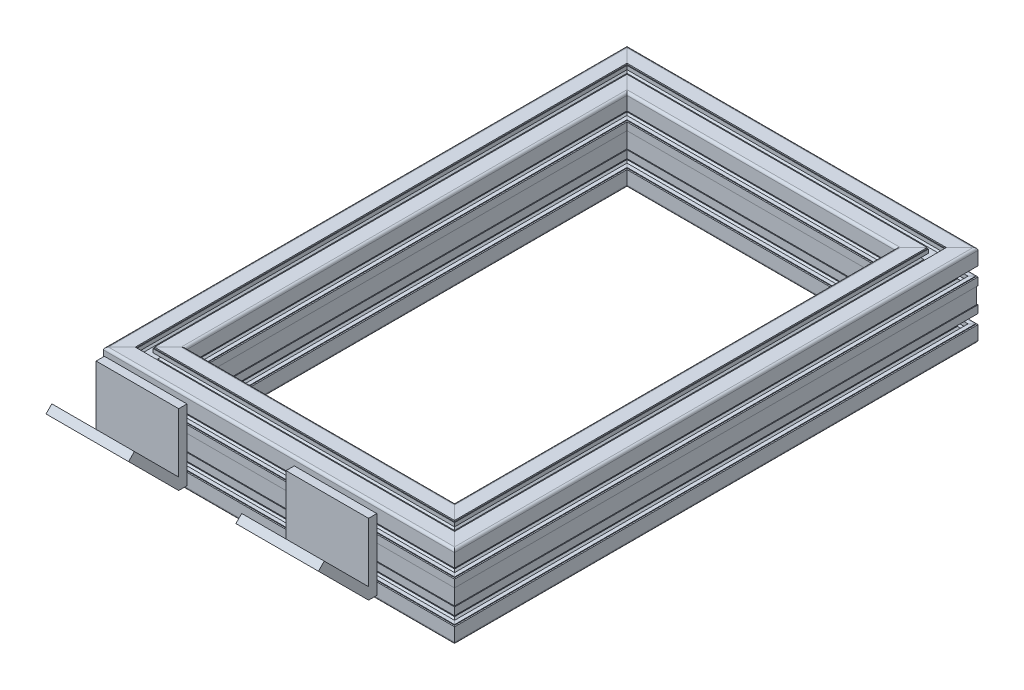
SolidWorks part; units mm, degrees
ref_plane "Plano frontal" through (0, 0, 0) normal (0, 0, 1) x (1, 0, 0)
ref_plane "Plano superior" through (0, 0, 0) normal (0, 1, 0) x (1, 0, 0)
ref_plane "Plano direito" through (0, 0, 0) normal (1, 0, 0) x (0, 0, -1)
sketch3d "3DSketch1"
  line L0 (-22674.7588, 3641.8152, 40199.9002) -> (-22776.7588, 3641.8152, 40199.9002) construction
  line L1 (-22674.7588, 12271.8152, 40199.9002) -> (-22674.7588, -2728.1848, 40199.9002) construction
  line L2 (-22776.7588, 12271.8152, 40199.9002) -> (-22776.7588, -2728.1848, 40199.9002) construction
  line L3 (-22676.9563, 3641.8152, 40224.9002) -> (-22676.9563, 3641.8152, 40808.9455)
  line L4 (-22676.9563, 3641.8152, 40808.9455) -> (-23052.1444, 3641.8152, 40808.9455)
  line L5 (-23052.1444, 3641.8152, 40808.9455) -> (-23052.1444, 3641.8152, 40224.9002)
  line L6 (-22676.9563, 3641.8152, 40224.9002) -> (-23052.1444, 3641.8152, 40224.9002)
  line L7 (-22872.616, 3641.8152, 40199.9002) -> (-22872.616, 3641.8152, 40224.9002) construction
  line L8 (-22776.9563, 3641.8152, 40706.6002) -> (-22776.9563, 3641.8152, 40224.9002) construction
  line L9 (-22776.9563, 11646.2158, 40706.6002) -> (-22776.9563, -2011.9888, 40706.6002) construction
  line L10 (-22902.1444, 3641.8152, 40306.6002) -> (-22902.1444, 3641.8152, 40224.9002) construction
  line L12 (-22776.9563, 3641.8152, 40706.6002) -> (-22902.1444, 3641.8152, 40706.6002) construction
  line L13 (-22902.1444, 3641.8152, 40706.6002) -> (-22902.1444, 3641.8152, 40306.6002) construction
  line L14 (-22902.1444, 11499.48, 40306.6002) -> (-22902.1444, -1887.3148, 40306.6002) construction
  dimension "D1" = 25
  dimension "D2" = 100
  dimension "D3" = 150
other "Aluminium profile 50x100 50X100(1)"
ref_plane "Plane1" through (-22676.9563, 3641.8152, 40224.9002) normal (0, 0, 1) x (1, 0, 0)
sketch "Sketch1" plane through (-22676.9563, 3641.8152, 40224.9002) normal (0, 0, 1) x (1, 0, 0)
  line L0 (15.1906, 37.8447) -> (11.8847, 34.5389)
  line L1 (11.8847, 34.5389) -> (9.5389, 36.8847)
  line L2 (9.5389, 36.8847) -> (12.8447, 40.1906)
  line L3 (11.2262, 45.7) -> (9.5, 45.7)
  line L4 (9.5, 45.7) -> (9.5, 48.3)
  line L5 (9.5, 48.3) -> (19, 48.3)
  line L6 (19, 48.3) -> (19, 47.2697)
  line L7 (22.2697, 44) -> (23.3, 44)
  line L8 (23.3, 44) -> (23.3, 34.5)
  line L9 (23.3, 34.5) -> (20.7, 34.5)
  line L10 (20.7, 34.5) -> (20.7, 36.2262)
  line L11 (12.8447, -40.1906) -> (9.5389, -36.8847)
  line L12 (9.5389, -36.8847) -> (11.8847, -34.5389)
  line L13 (11.8847, -34.5389) -> (15.1906, -37.8447)
  line L14 (20.7, -36.2262) -> (20.7, -34.5)
  line L15 (20.7, -34.5) -> (23.3, -34.5)
  line L16 (23.3, -34.5) -> (23.3, -44)
  line L17 (23.3, -44) -> (22.2697, -44)
  line L18 (19, -47.2697) -> (19, -48.3)
  line L19 (19, -48.3) -> (9.5, -48.3)
  line L20 (9.5, -48.3) -> (9.5, -45.7)
  line L21 (9.5, -45.7) -> (11.2262, -45.7)
  line L22 (-19, 48.3) -> (-9.5, 48.3)
  line L23 (-9.5, 48.3) -> (-9.5, 45.7)
  line L24 (-9.5, 45.7) -> (-11.2262, 45.7)
  line L25 (-12.8447, 40.1906) -> (-9.5389, 36.8847)
  line L26 (-9.5389, 36.8847) -> (-11.8847, 34.5389)
  line L27 (-11.8847, 34.5389) -> (-15.1906, 37.8447)
  line L28 (-20.7, 36.2262) -> (-20.7, 34.5)
  line L29 (-20.7, 34.5) -> (-23.3, 34.5)
  line L30 (-23.3, 34.5) -> (-23.3, 44)
  line L31 (-23.3, 44) -> (-22.2697, 44)
  line L32 (-19, 47.2697) -> (-19, 48.3)
  line L33 (-23.3, -34.5) -> (-20.7, -34.5)
  line L34 (-20.7, -34.5) -> (-20.7, -36.2262)
  line L35 (-15.1906, -37.8447) -> (-11.8847, -34.5389)
  line L36 (-11.8847, -34.5389) -> (-9.5389, -36.8847)
  line L37 (-9.5389, -36.8847) -> (-12.8447, -40.1906)
  line L38 (-11.2262, -45.7) -> (-9.5, -45.7)
  line L39 (-9.5, -45.7) -> (-9.5, -48.3)
  line L40 (-9.5, -48.3) -> (-19, -48.3)
  line L41 (-19, -48.3) -> (-19, -47.2697)
  line L42 (-22.2697, -44) -> (-23.3, -44)
  line L43 (-23.3, -44) -> (-23.3, -34.5)
  line L44 (-10.3, -23) -> (-10.3, -16.9877)
  line L45 (-10.3, -16.9877) -> (-8.0123, -14.7)
  line L46 (-8.0123, -14.7) -> (-2, -14.7)
  line L47 (-2, -14.7) -> (-2, -16.5539)
  line L48 (-2, -16.5539) -> (-3.5923, -17.2964)
  line L49 (-3.5923, -17.2964) -> (-2.1131, -20.4685)
  line L50 (2.1131, -20.4685) -> (3.5923, -17.2964)
  line L51 (3.5923, -17.2964) -> (2, -16.5539)
  line L52 (2, -16.5539) -> (2, -14.7)
  line L53 (2, -14.7) -> (8.0123, -14.7)
  line L54 (8.0123, -14.7) -> (10.3, -16.9877)
  line L55 (10.3, -16.9877) -> (10.3, -23)
  line L56 (10.3, -23) -> (8.4461, -23)
  line L57 (8.4461, -23) -> (7.7036, -21.4077)
  line L58 (7.7036, -21.4077) -> (4.5315, -22.8869)
  line L59 (4.5315, -27.1131) -> (7.7036, -28.5923)
  line L60 (7.7036, -28.5923) -> (8.4461, -27)
  line L61 (8.4461, -27) -> (10.3, -27)
  line L62 (10.3, -27) -> (10.3, -33.0123)
  line L63 (10.3, -33.0123) -> (8.0123, -35.3)
  line L64 (8.0123, -35.3) -> (2, -35.3)
  line L65 (2, -35.3) -> (2, -33.4461)
  line L66 (2, -33.4461) -> (3.5923, -32.7036)
  line L67 (3.5923, -32.7036) -> (2.1131, -29.5315)
  line L68 (-2.1131, -29.5315) -> (-3.5923, -32.7036)
  line L69 (-3.5923, -32.7036) -> (-2, -33.4461)
  line L70 (-2, -33.4461) -> (-2, -35.3)
  line L71 (-2, -35.3) -> (-8.0123, -35.3)
  line L72 (-8.0123, -35.3) -> (-10.3, -33.0123)
  line L73 (-10.3, -33.0123) -> (-10.3, -27)
  line L74 (-10.3, -27) -> (-8.4461, -27)
  line L75 (-8.4461, -27) -> (-7.7036, -28.5923)
  line L76 (-7.7036, -28.5923) -> (-4.5315, -27.1131)
  line L77 (-4.5315, -22.8869) -> (-7.7036, -21.4077)
  line L78 (-7.7036, -21.4077) -> (-8.4461, -23)
  line L79 (-8.4461, -23) -> (-10.3, -23)
  line L80 (8.0123, 35.3) -> (10.3, 33.0123)
  line L81 (10.3, 33.0123) -> (10.3, 27)
  line L82 (10.3, 27) -> (8.4461, 27)
  line L83 (8.4461, 27) -> (7.7036, 28.5923)
  line L84 (7.7036, 28.5923) -> (4.5315, 27.1131)
  line L85 (4.5315, 22.8869) -> (7.7036, 21.4077)
  line L86 (7.7036, 21.4077) -> (8.4461, 23)
  line L87 (8.4461, 23) -> (10.3, 23)
  line L88 (10.3, 23) -> (10.3, 16.9877)
  line L89 (10.3, 16.9877) -> (8.0123, 14.7)
  line L90 (8.0123, 14.7) -> (2, 14.7)
  line L91 (2, 14.7) -> (2, 16.5539)
  line L92 (2, 16.5539) -> (3.5923, 17.2964)
  line L93 (3.5923, 17.2964) -> (2.1131, 20.4685)
  line L94 (-2.1131, 20.4685) -> (-3.5923, 17.2964)
  line L95 (-3.5923, 17.2964) -> (-2, 16.5539)
  line L96 (-2, 16.5539) -> (-2, 14.7)
  line L97 (-2, 14.7) -> (-8.0123, 14.7)
  line L98 (-8.0123, 14.7) -> (-10.3, 16.9877)
  line L99 (-10.3, 16.9877) -> (-10.3, 23)
  line L100 (-10.3, 23) -> (-8.4461, 23)
  line L101 (-8.4461, 23) -> (-7.7036, 21.4077)
  line L102 (-7.7036, 21.4077) -> (-4.5315, 22.8869)
  line L103 (-4.5315, 27.1131) -> (-7.7036, 28.5923)
  line L104 (-7.7036, 28.5923) -> (-8.4461, 27)
  line L105 (-8.4461, 27) -> (-10.3, 27)
  line L106 (-10.3, 27) -> (-10.3, 33.0123)
  line L107 (-10.3, 33.0123) -> (-8.0123, 35.3)
  line L108 (-8.0123, 35.3) -> (-2, 35.3)
  line L109 (-2, 35.3) -> (-2, 33.4461)
  line L110 (-2, 33.4461) -> (-3.5923, 32.7036)
  line L111 (-3.5923, 32.7036) -> (-2.1131, 29.5315)
  line L112 (2.1131, 29.5315) -> (3.5923, 32.7036)
  line L113 (3.5923, 32.7036) -> (2, 33.4461)
  line L114 (2, 33.4461) -> (2, 35.3)
  line L115 (2, 35.3) -> (8.0123, 35.3)
  line L116 (21, 12.45) -> (21, -12.45)
  line L117 (21, -12.45) -> (-21, -12.45)
  line L118 (-21, -12.45) -> (-21, 12.45)
  line L119 (-21, 12.45) -> (21, 12.45)
  line L120 (23.5, -30) -> (19, -30)
  line L121 (19, -30) -> (19, -35.05)
  line L122 (19, -35.05) -> (14.8, -35.05)
  line L123 (14.8, -35.05) -> (12.5, -32.75)
  line L124 (12.5, -32.75) -> (12.5, -17.25)
  line L125 (12.5, -17.25) -> (14.8, -14.95)
  line L126 (14.8, -14.95) -> (19, -14.95)
  line L127 (19, -14.95) -> (19, -20)
  line L128 (19, -20) -> (23.5, -20)
  line L129 (23.5, -20) -> (23.5, -19.2)
  line L130 (23.5, -19.2) -> (25, -19.2)
  line L131 (25, -19.2) -> (25, -10)
  line L132 (25, -10) -> (24, -10)
  line L133 (24, -10) -> (24, 10)
  line L134 (24, 10) -> (25, 10)
  line L135 (25, 10) -> (25, 19.2)
  line L136 (25, 19.2) -> (23.5, 19.2)
  line L137 (23.5, 19.2) -> (23.5, 20)
  line L138 (23.5, 20) -> (19, 20)
  line L139 (19, 20) -> (19, 14.95)
  line L140 (19, 14.95) -> (14.8, 14.95)
  line L141 (14.8, 14.95) -> (12.5, 17.25)
  line L142 (12.5, 17.25) -> (12.5, 32.75)
  line L143 (12.5, 32.75) -> (14.8, 35.05)
  line L144 (14.8, 35.05) -> (19, 35.05)
  line L145 (19, 35.05) -> (19, 30)
  line L146 (19, 30) -> (23.5, 30)
  line L147 (23.5, 30) -> (23.5, 30.8)
  line L148 (23.5, 30.8) -> (25, 30.8)
  line L149 (25, 30.8) -> (25, 47)
  line L150 (22, 50) -> (5.8, 50)
  line L151 (5.8, 50) -> (5.8, 48.5)
  line L152 (5.8, 48.5) -> (5, 48.5)
  line L153 (5, 48.5) -> (5, 44)
  line L154 (5, 44) -> (10.05, 44)
  line L155 (10.05, 44) -> (10.05, 39.8)
  line L156 (10.05, 39.8) -> (7.75, 37.5)
  line L157 (7.75, 37.5) -> (-7.75, 37.5)
  line L158 (-7.75, 37.5) -> (-10.05, 39.8)
  line L159 (-10.05, 39.8) -> (-10.05, 44)
  line L160 (-10.05, 44) -> (-5, 44)
  line L161 (-5, 44) -> (-5, 48.5)
  line L162 (-5, 48.5) -> (-5.8, 48.5)
  line L163 (-5.8, 48.5) -> (-5.8, 50)
  line L164 (-5.8, 50) -> (-22, 50)
  line L165 (-25, 47) -> (-25, 30.8)
  line L166 (-25, 30.8) -> (-23.5, 30.8)
  line L167 (-23.5, 30.8) -> (-23.5, 30)
  line L168 (-23.5, 30) -> (-19, 30)
  line L169 (-19, 30) -> (-19, 35.05)
  line L170 (-19, 35.05) -> (-14.8, 35.05)
  line L171 (-14.8, 35.05) -> (-12.5, 32.75)
  line L172 (-12.5, 32.75) -> (-12.5, 17.25)
  line L173 (-12.5, 17.25) -> (-14.8, 14.95)
  line L174 (-14.8, 14.95) -> (-19, 14.95)
  line L175 (-19, 14.95) -> (-19, 20)
  line L176 (-19, 20) -> (-23.5, 20)
  line L177 (-23.5, 20) -> (-23.5, 19.2)
  line L178 (-23.5, 19.2) -> (-25, 19.2)
  line L179 (-25, 19.2) -> (-25, 10)
  line L180 (-25, 10) -> (-24, 10)
  line L181 (-24, 10) -> (-24, -10)
  line L182 (-24, -10) -> (-25, -10)
  line L183 (-25, -10) -> (-25, -19.2)
  line L184 (-25, -19.2) -> (-23.5, -19.2)
  line L185 (-23.5, -19.2) -> (-23.5, -20)
  line L186 (-23.5, -20) -> (-19, -20)
  line L187 (-19, -20) -> (-19, -14.95)
  line L188 (-19, -14.95) -> (-14.8, -14.95)
  line L189 (-14.8, -14.95) -> (-12.5, -17.25)
  line L190 (-12.5, -17.25) -> (-12.5, -32.75)
  line L191 (-12.5, -32.75) -> (-14.8, -35.05)
  line L192 (-14.8, -35.05) -> (-19, -35.05)
  line L193 (-19, -35.05) -> (-19, -30)
  line L194 (-19, -30) -> (-23.5, -30)
  line L195 (-23.5, -30) -> (-23.5, -30.8)
  line L196 (-23.5, -30.8) -> (-25, -30.8)
  line L197 (-25, -30.8) -> (-25, -47)
  line L198 (-22, -50) -> (-5.8, -50)
  line L199 (-5.8, -50) -> (-5.8, -48.5)
  line L200 (-5.8, -48.5) -> (-5, -48.5)
  line L201 (-5, -48.5) -> (-5, -44)
  line L202 (-5, -44) -> (-10.05, -44)
  line L203 (-10.05, -44) -> (-10.05, -39.8)
  line L204 (-10.05, -39.8) -> (-7.75, -37.5)
  line L205 (-7.75, -37.5) -> (7.75, -37.5)
  line L206 (7.75, -37.5) -> (10.05, -39.8)
  line L207 (10.05, -39.8) -> (10.05, -44)
  line L208 (10.05, -44) -> (5, -44)
  line L209 (5, -44) -> (5, -48.5)
  line L210 (5, -48.5) -> (5.8, -48.5)
  line L211 (5.8, -48.5) -> (5.8, -50)
  line L212 (5.8, -50) -> (22, -50)
  line L213 (25, -47) -> (25, -30.8)
  line L214 (25, -30.8) -> (23.5, -30.8)
  line L215 (23.5, -30.8) -> (23.5, -30)
  arc A0 (15.5214, 37.9081) -> (15.1906, 37.8447) centre (15.4027, 37.6326) ccw
  arc A1 (12.8447, 40.1906) -> (12.9081, 40.5214) centre (12.6326, 40.4027) ccw
  arc A2 (12.9081, 40.5214) -> (12.674, 43.8077) centre (17.5, 42.5) cw
  arc A3 (12.674, 43.8077) -> (11.2262, 45.7) centre (11.2262, 44.2) ccw
  arc A4 (19, 47.2697) -> (22.2697, 44) centre (17.5, 42.5) cw
  arc A5 (20.7, 36.2262) -> (18.8077, 37.674) centre (19.2, 36.2262) ccw
  arc A6 (18.8077, 37.674) -> (15.5214, 37.9081) centre (17.5, 42.5) cw
  arc A7 (15.1906, -37.8447) -> (15.5214, -37.9081) centre (15.4027, -37.6326) ccw
  arc A8 (15.5214, -37.9081) -> (18.8077, -37.674) centre (17.5, -42.5) cw
  arc A9 (18.8077, -37.674) -> (20.7, -36.2262) centre (19.2, -36.2262) ccw
  arc A10 (22.2697, -44) -> (19, -47.2697) centre (17.5, -42.5) cw
  arc A11 (11.2262, -45.7) -> (12.674, -43.8077) centre (11.2262, -44.2) ccw
  arc A12 (12.674, -43.8077) -> (12.9081, -40.5214) centre (17.5, -42.5) cw
  arc A13 (12.9081, -40.5214) -> (12.8447, -40.1906) centre (12.6326, -40.4027) ccw
  arc A14 (-11.2262, 45.7) -> (-12.674, 43.8077) centre (-11.2262, 44.2) ccw
  arc A15 (-12.674, 43.8077) -> (-12.9081, 40.5214) centre (-17.5, 42.5) cw
  arc A16 (-12.9081, 40.5214) -> (-12.8447, 40.1906) centre (-12.6326, 40.4027) ccw
  arc A17 (-15.1906, 37.8447) -> (-15.5214, 37.9081) centre (-15.4027, 37.6326) ccw
  arc A18 (-15.5214, 37.9081) -> (-18.8077, 37.674) centre (-17.5, 42.5) cw
  arc A19 (-18.8077, 37.674) -> (-20.7, 36.2262) centre (-19.2, 36.2262) ccw
  arc A20 (-22.2697, 44) -> (-19, 47.2697) centre (-17.5, 42.5) cw
  arc A21 (-20.7, -36.2262) -> (-18.8077, -37.674) centre (-19.2, -36.2262) ccw
  arc A22 (-18.8077, -37.674) -> (-15.5214, -37.9081) centre (-17.5, -42.5) cw
  arc A23 (-15.5214, -37.9081) -> (-15.1906, -37.8447) centre (-15.4027, -37.6326) ccw
  arc A24 (-12.8447, -40.1906) -> (-12.9081, -40.5214) centre (-12.6326, -40.4027) ccw
  arc A25 (-12.9081, -40.5214) -> (-12.674, -43.8077) centre (-17.5, -42.5) cw
  arc A26 (-12.674, -43.8077) -> (-11.2262, -45.7) centre (-11.2262, -44.2) ccw
  arc A27 (-19, -47.2697) -> (-22.2697, -44) centre (-17.5, -42.5) cw
  arc A28 (-2.1131, -20.4685) -> (2.1131, -20.4685) centre (0, -25) cw
  arc A29 (4.5315, -22.8869) -> (4.5315, -27.1131) centre (0, -25) cw
  arc A30 (2.1131, -29.5315) -> (-2.1131, -29.5315) centre (0, -25) cw
  arc A31 (-4.5315, -27.1131) -> (-4.5315, -22.8869) centre (0, -25) cw
  arc A32 (4.5315, 27.1131) -> (4.5315, 22.8869) centre (0, 25) cw
  arc A33 (2.1131, 20.4685) -> (-2.1131, 20.4685) centre (0, 25) cw
  arc A34 (-4.5315, 22.8869) -> (-4.5315, 27.1131) centre (0, 25) cw
  arc A35 (-2.1131, 29.5315) -> (2.1131, 29.5315) centre (0, 25) cw
  arc A36 (25, 47) -> (22, 50) centre (22, 47) ccw
  arc A37 (-22, 50) -> (-25, 47) centre (-22, 47) ccw
  arc A38 (-25, -47) -> (-22, -50) centre (-22, -47) ccw
  arc A39 (22, -50) -> (25, -47) centre (22, -47) ccw
  point P282 (0, 0)
sketch "Sketch2" plane through (-23076.1444, 0, 0) normal (-1, 0, 0) x (0, 0, 1)
  line L0 (40843.9455, 3596.8439) -> (40904.6678, 3657.5662)
  line L1 (40843.9455, 3682.7182) -> (40833.9455, 3682.7182)
  line L2 (40843.9455, 3682.7182) -> (40843.9455, 3596.8439)
  line L3 (40843.9455, 3596.8439) -> (40833.9455, 3596.8439)
  line L4 (40833.9455, 3682.7182) -> (40833.9455, 3596.8439)
  line L5 (40904.6678, 3657.5662) -> (40897.5968, 3664.6373)
  line L6 (40897.5968, 3664.6373) -> (40843.9455, 3610.986)
  line L8 (40843.9455, 3610.986) -> (40843.9455, 3596.8439)
  line L9 (40833.9455, 3611.0152) -> (40833.9455, 3594.8152) construction
  dimension "D1" = 45
  dimension "D2" = 10
extrude "Boss-Extrude1" add sketch "Sketch2" against normal blind 100 separate body contours L5 L6 L2 L0 | L1 L4 L3 L2
pattern_linear "LPattern1" count 2 spacing 230 along (1, 0, 0) of "Boss-Extrude1"
